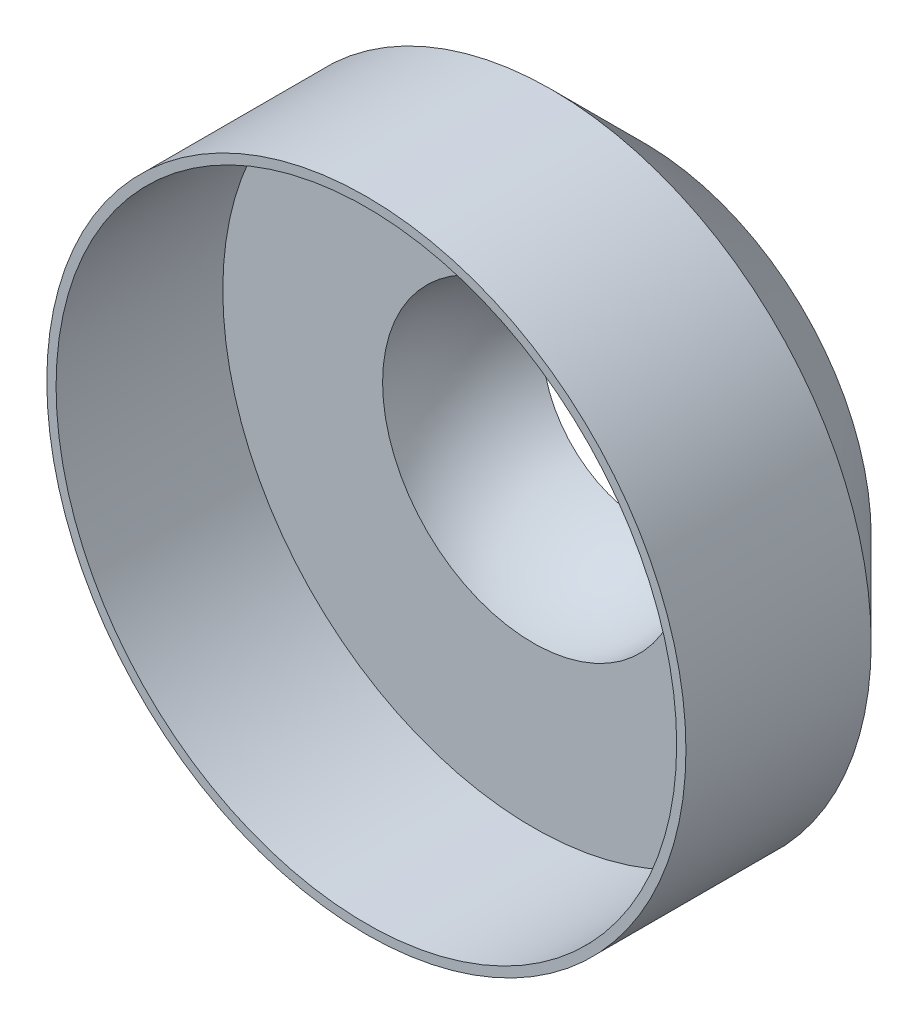
SolidWorks part; units mm, degrees
ref_plane "Front Plane" through (0, 0, 0) normal (0, 0, 1) x (1, 0, 0)
ref_plane "Top Plane" through (0, 0, 0) normal (0, 1, 0) x (1, 0, 0)
ref_plane "Right Plane" through (0, 0, 0) normal (1, 0, 0) x (0, 0, -1)
sketch "Sketch1" plane through (0, 0, 0) normal (0, 0, 1) x (1, 0, 0)
  circle A0 centre (0, 0) radius 34.5
  dimension "D1" = 69
extrude "Boss-Extrude1" add sketch "Sketch1" along normal blind 30
sketch "Sketch5" plane through (0, 0, 30) normal (0, 0, 1) x (1, 0, 0)
  circle A0 centre (0, 0) radius 33.5
  dimension "D1" = 67
extrude "Cut-Extrude2" cut sketch "Sketch5" against normal blind 18
ref_plane "Plane1" through (0, 0, 12) normal (0, 0, 1) x (1, 0, 0)
sketch "Sketch7" plane through (0, 0, 12) normal (0, 0, 1) x (1, 0, 0)
  line L0 (-16.25, 0) -> (16.25, 0)
  line L1 (0, 8.9792) -> (0, -9.4282) construction
  arc A0 (-16.25, 0) -> (16.25, 0) centre (0, 0) cw
  point P6 (0, 0)
  dimension "D1" = 32.5
revolve "Cut-Revolve3" cut sketch "Sketch7" angle 180 about L0
chamfer "Chamfer1" distance 10 angle 45 1 edges at (34.5, 0, 0)
